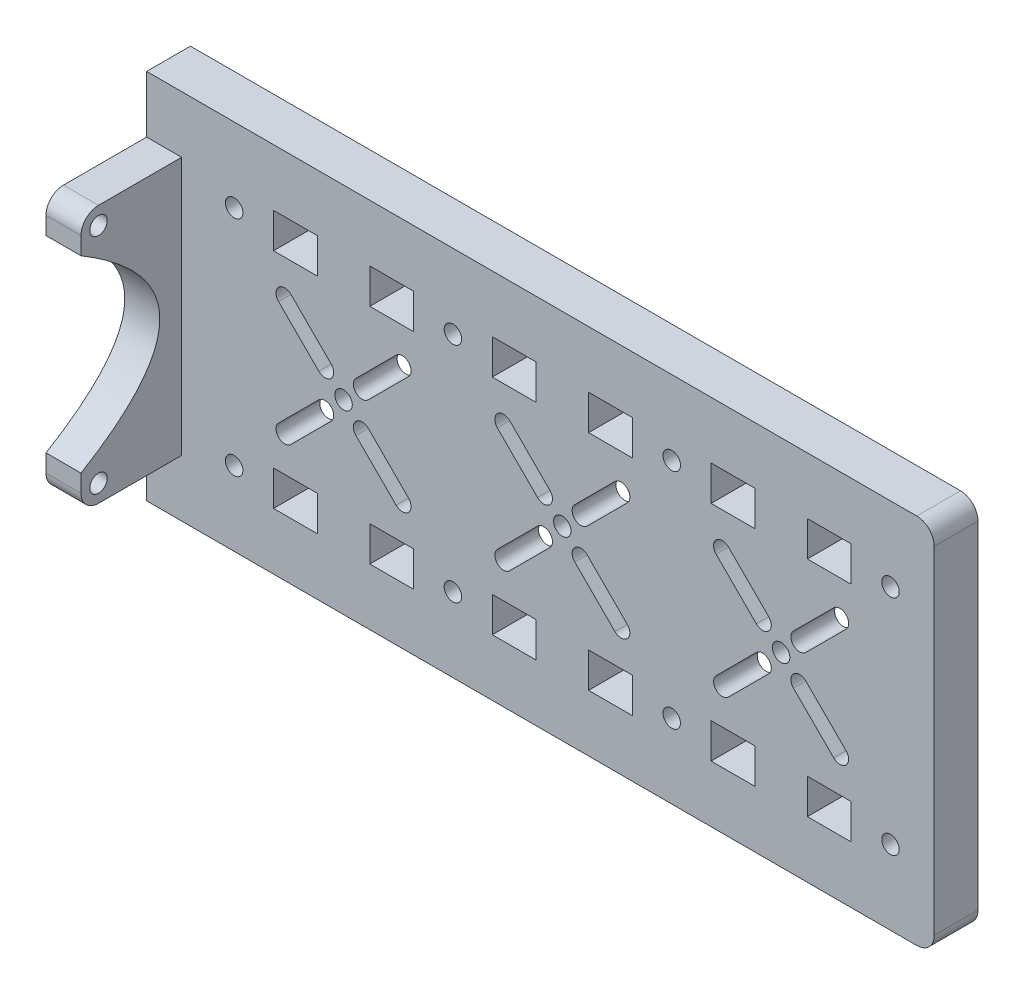
SolidWorks part; units mm, degrees
ref_plane "Ön Düzlem" through (0, 0, 0) normal (0, 0, 1) x (1, 0, 0)
ref_plane "Üst Düzlem" through (0, 0, 0) normal (0, 1, 0) x (1, 0, 0)
ref_plane "Sağ Düzlem" through (0, 0, 0) normal (1, 0, 0) x (0, 0, -1)
sketch "Çizim1" plane through (0, 0, 0) normal (0, 0, 1) x (1, 0, 0)
  line L1 (90, -42.5) -> (-90, -42.5)
  line L2 (90, -42.5) -> (90, 42.5)
  line L3 (90, 42.5) -> (-90, 42.5)
  line L4 (-90, -42.5) -> (-90, 42.5)
  line L5 (90, -42.5) -> (-90, 42.5) construction
  line L6 (90, 42.5) -> (-90, -42.5) construction
  point P0 (0, 0)
  dimension "D1" = 180
  dimension "D2" = 85
extrude "Yükseklik-Ekstrüzyon1" add sketch "Çizim1" along normal blind 10
ref_plane "Düzlem1" through (-90, 0, 0) normal (-1, 0, 0) x (0, 0, 1)
sketch "Çizim2" plane through (0, 0, 10) normal (0, 0, 1) x (1, 0, 0)
  line L0 (-90, 42.5) -> (-90, -42.5) construction
  line L1 (-61, -21.5) -> (-51, -21.5)
  line L2 (-61, -21.5) -> (-61, -29.5)
  line L3 (-61, -29.5) -> (-51, -29.5)
  line L4 (-51, -21.5) -> (-51, -29.5)
  line L5 (-59.8492, -12.0208) -> (-50.6569, -2.8284)
  line L6 (-45, 0) -> (-54.1887, -9.1887) construction
  line L7 (-39, -21.5) -> (-29, -21.5)
  line L8 (-39, -21.5) -> (-39, -29.5)
  line L9 (-39, -29.5) -> (-29, -29.5)
  line L10 (-29, -21.5) -> (-29, -29.5)
  line L11 (-57.0208, -14.8492) -> (-47.8284, -5.6569)
  line L15 (-45, 0) -> (-45, 9.9868) construction
  line L16 (0, 0) -> (-70.5168, 0) construction
  line L17 (-30.1508, -12.0208) -> (-39.3431, -2.8284)
  line L18 (-32.9792, -14.8492) -> (-42.1716, -5.6569)
  line L19 (-59.8492, 12.0208) -> (-50.6569, 2.8284)
  line L20 (-30.1508, 12.0208) -> (-39.3431, 2.8284)
  line L21 (-32.9792, 14.8492) -> (-42.1716, 5.6569)
  line L22 (-39, 29.5) -> (-29, 29.5)
  line L23 (-29, 21.5) -> (-29, 29.5)
  line L24 (-39, 21.5) -> (-29, 21.5)
  line L25 (-39, 21.5) -> (-39, 29.5)
  line L26 (-61, 29.5) -> (-51, 29.5)
  line L27 (-51, 21.5) -> (-51, 29.5)
  line L28 (-61, 21.5) -> (-51, 21.5)
  line L29 (-61, 21.5) -> (-61, 29.5)
  line L30 (-57.0208, 14.8492) -> (-47.8284, 5.6569)
  line L125 (-11, 29.5) -> (-1, 29.5)
  line L126 (-1, 21.5) -> (-1, 29.5)
  line L127 (-11, 21.5) -> (-1, 21.5)
  line L128 (-11, 21.5) -> (-11, 29.5)
  line L129 (11, 29.5) -> (21, 29.5)
  line L130 (21, 21.5) -> (21, 29.5)
  line L131 (11, 21.5) -> (21, 21.5)
  line L132 (11, 21.5) -> (11, 29.5)
  line L133 (-9.8492, 12.0208) -> (-0.6569, 2.8284)
  line L134 (-7.0208, 14.8492) -> (2.1716, 5.6569)
  line L135 (19.8492, 12.0208) -> (10.6569, 2.8284)
  line L136 (17.0208, 14.8492) -> (7.8284, 5.6569)
  line L137 (17.0208, -14.8492) -> (7.8284, -5.6569)
  line L138 (19.8492, -12.0208) -> (10.6569, -2.8284)
  line L139 (-9.8492, -12.0208) -> (-0.6569, -2.8284)
  line L140 (-7.0208, -14.8492) -> (2.1716, -5.6569)
  line L141 (-11, -21.5) -> (-11, -29.5)
  line L142 (-11, -21.5) -> (-1, -21.5)
  line L143 (-1, -21.5) -> (-1, -29.5)
  line L144 (-11, -29.5) -> (-1, -29.5)
  line L145 (11, -21.5) -> (11, -29.5)
  line L146 (11, -21.5) -> (21, -21.5)
  line L147 (21, -21.5) -> (21, -29.5)
  line L148 (11, -29.5) -> (21, -29.5)
  line L149 (39, 29.5) -> (49, 29.5)
  line L150 (49, 21.5) -> (49, 29.5)
  line L151 (39, 21.5) -> (49, 21.5)
  line L152 (39, 21.5) -> (39, 29.5)
  line L153 (61, 29.5) -> (71, 29.5)
  line L154 (71, 21.5) -> (71, 29.5)
  line L155 (61, 21.5) -> (71, 21.5)
  line L156 (61, 21.5) -> (61, 29.5)
  line L157 (40.1508, 12.0208) -> (49.3431, 2.8284)
  line L158 (42.9792, 14.8492) -> (52.1716, 5.6569)
  line L159 (69.8492, 12.0208) -> (60.6569, 2.8284)
  line L160 (67.0208, 14.8492) -> (57.8284, 5.6569)
  line L161 (67.0208, -14.8492) -> (57.8284, -5.6569)
  line L162 (69.8492, -12.0208) -> (60.6569, -2.8284)
  line L163 (40.1508, -12.0208) -> (49.3431, -2.8284)
  line L164 (42.9792, -14.8492) -> (52.1716, -5.6569)
  line L165 (39, -21.5) -> (39, -29.5)
  line L166 (39, -21.5) -> (49, -21.5)
  line L167 (49, -21.5) -> (49, -29.5)
  line L168 (39, -29.5) -> (49, -29.5)
  line L169 (61, -21.5) -> (61, -29.5)
  line L170 (61, -21.5) -> (71, -21.5)
  line L171 (71, -21.5) -> (71, -29.5)
  line L172 (61, -29.5) -> (71, -29.5)
  line L173 (90, -42.5) -> (90, 42.5) construction
  circle A0 centre (-70, -25.5) radius 2
  circle A2 centre (-45, 0) radius 2
  arc A4 (-59.8492, -12.0208) -> (-57.0208, -14.8492) centre (-58.435, -13.435) ccw
  arc A6 (-47.8284, -5.6569) -> (-50.6569, -2.8284) centre (-49.2426, -4.2426) ccw
  arc A7 (-30.1508, -12.0208) -> (-32.9792, -14.8492) centre (-31.565, -13.435) cw
  arc A8 (-42.1716, -5.6569) -> (-39.3431, -2.8284) centre (-40.7574, -4.2426) cw
  arc A9 (-47.8284, 5.6569) -> (-50.6569, 2.8284) centre (-49.2426, 4.2426) cw
  arc A10 (-59.8492, 12.0208) -> (-57.0208, 14.8492) centre (-58.435, 13.435) cw
  arc A11 (-42.1716, 5.6569) -> (-39.3431, 2.8284) centre (-40.7574, 4.2426) ccw
  arc A12 (-30.1508, 12.0208) -> (-32.9792, 14.8492) centre (-31.565, 13.435) ccw
  circle A13 centre (-70, 25.5) radius 2
  circle A36 centre (80, 25.5) radius 2
  circle A37 centre (80, -25.5) radius 2
  circle A60 centre (-20, 25.5) radius 2
  arc A61 (2.1716, 5.6569) -> (-0.6569, 2.8284) centre (0.7574, 4.2426) cw
  arc A62 (-9.8492, 12.0208) -> (-7.0208, 14.8492) centre (-8.435, 13.435) cw
  arc A63 (7.8284, 5.6569) -> (10.6569, 2.8284) centre (9.2426, 4.2426) ccw
  arc A64 (19.8492, 12.0208) -> (17.0208, 14.8492) centre (18.435, 13.435) ccw
  circle A65 centre (5, 0) radius 2
  arc A66 (19.8492, -12.0208) -> (17.0208, -14.8492) centre (18.435, -13.435) cw
  arc A67 (7.8284, -5.6569) -> (10.6569, -2.8284) centre (9.2426, -4.2426) cw
  arc A68 (2.1716, -5.6569) -> (-0.6569, -2.8284) centre (0.7574, -4.2426) ccw
  arc A69 (-9.8492, -12.0208) -> (-7.0208, -14.8492) centre (-8.435, -13.435) ccw
  circle A70 centre (-20, -25.5) radius 2
  circle A71 centre (30, 25.5) radius 2
  arc A72 (52.1716, 5.6569) -> (49.3431, 2.8284) centre (50.7574, 4.2426) cw
  arc A73 (40.1508, 12.0208) -> (42.9792, 14.8492) centre (41.565, 13.435) cw
  arc A74 (57.8284, 5.6569) -> (60.6569, 2.8284) centre (59.2426, 4.2426) ccw
  arc A75 (69.8492, 12.0208) -> (67.0208, 14.8492) centre (68.435, 13.435) ccw
  circle A76 centre (55, 0) radius 2
  arc A77 (69.8492, -12.0208) -> (67.0208, -14.8492) centre (68.435, -13.435) cw
  arc A78 (57.8284, -5.6569) -> (60.6569, -2.8284) centre (59.2426, -4.2426) cw
  arc A79 (52.1716, -5.6569) -> (49.3431, -2.8284) centre (50.7574, -4.2426) ccw
  arc A80 (40.1508, -12.0208) -> (42.9792, -14.8492) centre (41.565, -13.435) ccw
  circle A81 centre (30, -25.5) radius 2
  dimension "D11" = 4
  dimension "D13" = 6
  dimension "D14" = 4
  dimension "D17" = 2
  dimension "D19" = 4
  dimension "D25" = 4
  dimension "D26" = 4
  dimension "D1" = 29
  dimension "D2" = 29.5
  dimension "D3" = 8
  dimension "D4" = 29.5
  dimension "D5" = 8
  dimension "D6" = 10
  dimension "D7" = 10
  dimension "D8" = 12
  dimension "D9" = 4
  dimension "D10" = 9
  dimension "D12" = 45
  dimension "D15" = 45
  dimension "D16" = 6
  dimension "D18" = 13
  dimension "D20" = 13
  dimension "D21" = 13
  dimension "D22" = 90
  dimension "D24" = 35
  dimension "D27" = 9
  dimension "D28" = 9
  dimension "D29" = 25.5
  dimension "D30" = 25.5
  dimension "D23" = 3
extrude "Kes-Ekstrüzyon1" cut sketch "Çizim2" against normal blind 10
sketch "Çizim3" plane through (0, 0, 0) normal (0, 0, -1) x (-1, 0, 0)
  line L0 (-90, -42.5) -> (-90, 42.5) construction
  circle A0 centre (70, 25.5) radius 5
  circle A1 centre (70, -25.5) radius 4.5
  circle A2 centre (20, 25.5) radius 5
  circle A3 centre (20, -25.5) radius 4.5
  circle A4 centre (-30, 25.5) radius 5
  circle A5 centre (-30, -25.5) radius 4.5
  circle A6 centre (-80, 25.5) radius 5
  circle A7 centre (-80, -25.5) radius 4.5
  dimension "D1" = 10
  dimension "D2" = 9
  dimension "D4" = 10
  dimension "D3" = 4
extrude "Kes-Ekstrüzyon2" cut sketch "Çizim3" against normal blind 5
sketch "Sketch1" plane through (-90, 0, 0) normal (-1, 0, 0) x (0, 0, 1)
  line L0 (10, 42.5) -> (10, -42.5) construction
  line L1 (10, -29.5) -> (33, -29.5)
  line L4 (33, -29.5) -> (33, -21.5)
  line L5 (10, 29.5) -> (33, 29.5)
  line L6 (33, 29.5) -> (33, 21.5)
  line L8 (10, 29.5) -> (10, -29.5)
  circle A0 centre (29, -25.5) radius 2
  circle A1 centre (29, 25.5) radius 2
  spline S0 degree 2 poles (33, 21.5) (-3, 0) (33, -21.5) knots 0 0 0 1 1 1
  dimension "D11" = 4
  dimension "D14" = 4
  dimension "D1" = 23
  dimension "D2" = 8
  dimension "D3" = 13
  dimension "D4" = 13
  dimension "D5" = 23
  dimension "D6" = 8
  dimension "D7" = 5
  dimension "D8" = 42.5
  dimension "D9" = 4
  dimension "D10" = 4
  dimension "D12" = 4
  dimension "D13" = 4
extrude "Boss-Extrude1" add sketch "Sketch1" against normal blind 8
fillet "Fillet1" radius 4 4 edges at (90, 42.5, 5) (90, -42.5, 5) (-86, 29.5, 33) (-86, -29.5, 33)
